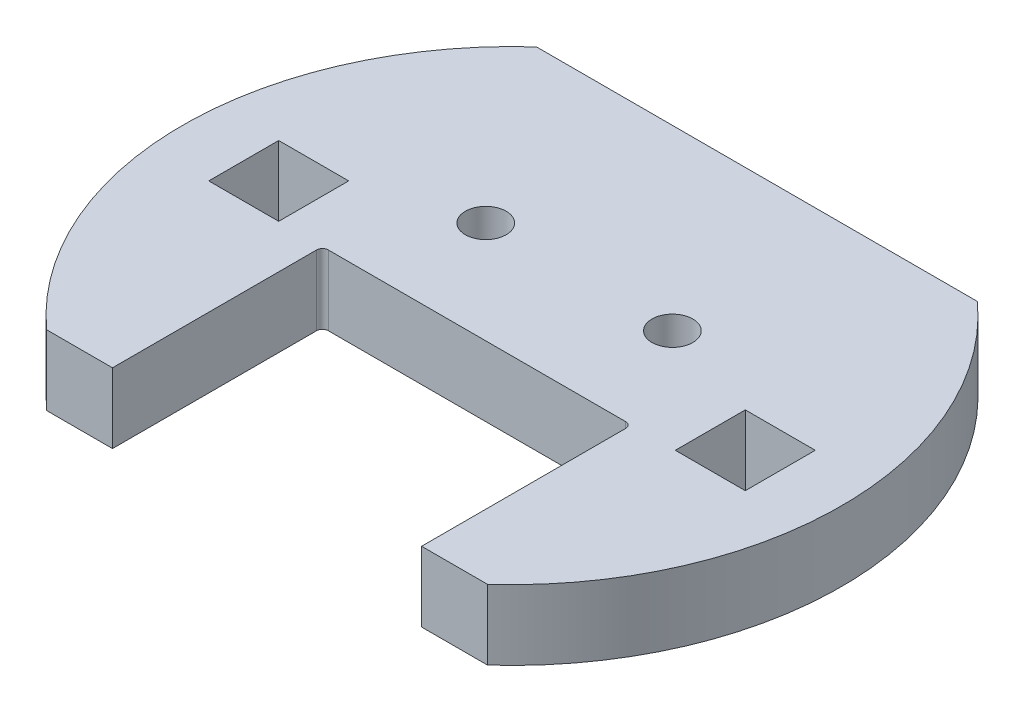
SolidWorks part; units mm, degrees
ref_plane "Alzado" through (0, 0, 0) normal (0, 0, 1) x (1, 0, 0)
ref_plane "Planta" through (0, 0, 0) normal (0, 1, 0) x (1, 0, 0)
ref_plane "Vista lateral" through (0, 0, 0) normal (1, 0, 0) x (0, 0, -1)
sketch "Croquis1" plane through (0, 0, 0) normal (0, 1, 0) x (1, 0, 0)
  line L0 (-161, 103.5) -> (-38.7919, 9.7565)
  line L1 (-40, 40) -> (40, 40) construction
  line L2 (-40, 40) -> (-40, -40) construction
  line L3 (-40, -40) -> (40, -40) construction
  line L4 (40, 40) -> (40, -40) construction
  line L5 (-40, 40) -> (40, -40) construction
  line L6 (-40, -40) -> (40, 40) construction
  line L7 (-161, 123.5) -> (161, 123.5) construction
  line L8 (-161, 123.5) -> (-161, -123.5) construction
  line L9 (-161, -123.5) -> (161, -123.5) construction
  line L10 (161, 123.5) -> (161, -123.5) construction
  line L11 (-161, 123.5) -> (161, -123.5) construction
  line L12 (-161, -123.5) -> (161, 123.5) construction
  line L13 (-161, 103.5) -> (-161, 123.5)
  line L14 (-161, 123.5) -> (-141, 123.5)
  line L15 (-141, 123.5) -> (-22.8238, 32.8493)
  line L16 (-38.7919, -9.7565) -> (-161, -103.5)
  line L17 (-161, -103.5) -> (-161, -123.5)
  line L18 (-161, -123.5) -> (-141, -123.5)
  line L19 (-141, -123.5) -> (-22.8238, -32.8493)
  line L20 (-38.7919, 9.7565) -> (-38.7919, -9.7565) construction
  line L21 (-22.8238, 32.8493) -> (-22.8238, -32.8493) construction
  line L22 (0, 40) -> (0, -40) construction
  line L23 (161, 123.5) -> (141, 123.5)
  line L24 (141, 123.5) -> (22.8238, 32.8493)
  line L25 (161, 103.5) -> (161, 123.5)
  line L26 (161, 103.5) -> (38.7919, 9.7565)
  line L27 (161, -123.5) -> (141, -123.5)
  line L28 (161, -103.5) -> (161, -123.5)
  line L29 (38.7919, -9.7565) -> (161, -103.5)
  line L30 (141, -123.5) -> (22.8238, -32.8493)
  circle A0 centre (0, 0) radius 40 construction
  arc A1 (-38.7919, 9.7565) -> (-38.7919, -9.7565) centre (0, 0) ccw
  arc A2 (-22.8238, 32.8493) -> (22.8238, 32.8493) centre (0, 0) cw
  arc A3 (22.8238, -32.8493) -> (-22.8238, -32.8493) centre (0, 0) cw
  arc A4 (38.7919, 9.7565) -> (38.7919, -9.7565) centre (0, 0) cw
  point P0 (0, 0)
  point P6 (0, 0)
  dimension "D1" = 80
  dimension "D2" = 80
  dimension "D3" = 322
  dimension "D4" = 247
  dimension "D5" = 20
extrude "Saliente-Extruir1" add sketch "Croquis1" along normal blind 6
sketch "Croquis4" plane through (0, 0, 0) normal (0, 1, 0) x (1, 0, 0)
  line L0 (-161, 103.5) -> (-161, 123.5)
  line L1 (-161, 123.5) -> (-141, 123.5)
  line L2 (-141, 123.5) -> (-141, 129.5)
  line L3 (-141, 129.5) -> (-167, 129.5)
  line L4 (-167, 129.5) -> (-167, 103.5)
  line L5 (-167, 103.5) -> (-161, 103.5)
  line L6 (-161, -103.5) -> (-161, -123.5)
  line L7 (-161, -123.5) -> (-141, -123.5)
  line L8 (-141, -123.5) -> (-141, -129.5)
  line L9 (-141, -129.5) -> (-167, -129.5)
  line L10 (-167, -129.5) -> (-167, -103.5)
  line L11 (-167, -103.5) -> (-161, -103.5)
  line L12 (0, 40) -> (0, -40) construction
  line L13 (167, -103.5) -> (161, -103.5)
  line L14 (167, -129.5) -> (167, -103.5)
  line L15 (141, -129.5) -> (167, -129.5)
  line L16 (141, -123.5) -> (141, -129.5)
  line L17 (161, -123.5) -> (141, -123.5)
  line L18 (161, -103.5) -> (161, -123.5)
  line L19 (167, 103.5) -> (161, 103.5)
  line L20 (167, 129.5) -> (167, 103.5)
  line L21 (141, 129.5) -> (167, 129.5)
  line L22 (141, 123.5) -> (141, 129.5)
  line L23 (161, 123.5) -> (141, 123.5)
  line L24 (161, 103.5) -> (161, 123.5)
  arc A0 (22.8238, 32.8493) -> (-22.8238, 32.8493) centre (0, 0) ccw construction
  arc A1 (-22.8238, -32.8493) -> (22.8238, -32.8493) centre (0, 0) ccw construction
  dimension "D1" = 6
  dimension "D2" = 6
  dimension "D3" = 6
  dimension "D4" = 6
extrude "Saliente-Extruir2" [suppressed] add sketch "Croquis4" along normal blind 12
sketch "Croquis7" plane through (0, 0, 0) normal (0, -1, 0) x (-1, 0, 0)
  circle A0 centre (0, 0) radius 40
  arc A1 (-38.7919, 9.7565) -> (-38.7919, -9.7565) centre (0, 0) ccw construction
extrude "Saliente-Extruir5" add sketch "Croquis7" along normal blind 6
sketch "Croquis5" plane through (0, -6, 0) normal (0, -1, 0) x (1, 0, 0)
  line L0 (13.25, 11) -> (-13.25, 11) construction
  line L1 (-10.25, 8) -> (10.25, 8) construction
  line L2 (-10.25, 8) -> (-10.25, -8) construction
  line L3 (-10.25, -8) -> (10.25, -8) construction
  line L4 (10.25, 8) -> (10.25, -8) construction
  line L5 (-10.25, 8) -> (10.25, -8) construction
  line L6 (-10.25, -8) -> (10.25, 8) construction
  line L7 (-13.25, 11) -> (-13.25, -11) construction
  line L8 (-13.25, -11) -> (13.25, -11) construction
  line L9 (13.25, -11) -> (13.25, -21) construction
  line L10 (13.25, -21) -> (-28.25, -21) construction
  line L11 (-28.25, -21) -> (-28.25, 21) construction
  line L12 (-28.25, 21) -> (13.25, 21) construction
  line L13 (13.25, 21) -> (13.25, 11) construction
  line L14 (0, 11) -> (0, 0) construction
  line L15 (0, 0) -> (0, -11) construction
  line L16 (13.25, 11) -> (28.25, 11) construction
  line L17 (-28.25, 21) -> (28.25, 21) construction
  line L18 (-28.25, 21) -> (-28.25, -21) construction
  line L19 (-28.25, -21) -> (28.25, -21) construction
  line L20 (28.25, 21) -> (28.25, -21) construction
  line L21 (-28.25, 21) -> (28.25, -21) construction
  line L22 (-28.25, -21) -> (28.25, 21) construction
  line L23 (28.25, 11) -> (28.25, 21) construction
  line L24 (28.25, 21) -> (13.25, 21) construction
  line L25 (13.25, -21) -> (28.25, -21) construction
  line L26 (28.25, -21) -> (28.25, -11) construction
  line L27 (28.25, -11) -> (13.25, -11) construction
  line L28 (-9, 7) -> (9, 7) construction
  line L29 (0, 7) -> (0, 0) construction
  line L30 (-9, 7) -> (9, 7) construction
  line L31 (-9, 7.5) -> (9, 7.5) construction
  line L32 (-9, 6.5) -> (9, 6.5) construction
  line L33 (-18.8961, 21) -> (18.8961, 21) construction
  line L34 (18.8961, -21) -> (-18.8961, -21)
  line L35 (-18.8961, 21) -> (-13.25, 21)
  line L36 (-13.25, 21) -> (-13.25, -11)
  line L37 (-13.25, -11) -> (13.25, -11)
  line L38 (13.25, -11) -> (13.25, 21)
  line L39 (13.25, 21) -> (18.8961, 21)
  line L40 (-8, -5.75) -> (8, -5.75) construction
  arc A0 (-9, 7.5) -> (-9, 6.5) centre (-9, 7) ccw construction
  arc A1 (9, 6.5) -> (9, 7.5) centre (9, 7) ccw construction
  arc A2 (-18.8961, 21) -> (-18.8961, -21) centre (0, 0) ccw
  arc A3 (18.8961, 21) -> (18.8961, -21) centre (0, 0) cw
  circle A4 centre (-8, -5.75) radius 1.75 construction
  circle A5 centre (8, -5.75) radius 1.75 construction
  point P0 (0, 0)
  point P26 (0, 7)
  dimension "D11" = 0.5
  dimension "D12" = 3.5
  dimension "D14" = 2.25
  dimension "D1" = 16
  dimension "D2" = 20.5
  dimension "D3" = 3
  dimension "D4" = 3
  dimension "D5" = 10
  dimension "D6" = 10
  dimension "D7" = 15
  dimension "D8" = 3
  dimension "D9" = 18
  dimension "D10" = 1
  dimension "D13" = 2.25
  dimension "D15" = 2.25
extrude "Saliente-Extruir3" add sketch "Croquis5" along normal blind 6
sketch "Croquis6" plane through (0, -12, 0) normal (0, -1, 0) x (1, 0, 0)
  line L0 (18.8961, 21) -> (13.25, 21) construction
  line L1 (-28.25, 21) -> (28.25, 21) construction
  line L2 (-28.25, 21) -> (-28.25, -21) construction
  line L3 (-28.25, -21) -> (28.25, -21) construction
  line L4 (28.25, 21) -> (28.25, -21) construction
  line L5 (-28.25, 21) -> (28.25, -21) construction
  line L6 (-28.25, -21) -> (28.25, 21) construction
  line L7 (-18.8961, 21) -> (-13.25, 21)
  line L8 (-9, 7) -> (9, 7) construction
  line L9 (-9, 7.5) -> (9, 7.5) construction
  line L10 (-9, 6.5) -> (9, 6.5) construction
  line L11 (-18.8961, 21) -> (18.8961, 21) construction
  line L12 (18.8961, -21) -> (-18.8961, -21) construction
  line L18 (13.25, 21) -> (18.8961, 21)
  line L19 (18.8961, -21) -> (-18.8961, -21)
  line L20 (-13.25, 21) -> (-13.25, 3.5)
  line L21 (-13.25, 21) -> (-13.25, -11) construction
  line L22 (-12.75, 3) -> (12.75, 3)
  line L23 (13.25, -11) -> (13.25, 21) construction
  line L24 (13.25, 3.5) -> (13.25, 21)
  line L25 (-13.25, 3.5) -> (13.25, 3.5) construction
  arc A0 (-9, 7.5) -> (-9, 6.5) centre (-9, 7) ccw construction
  arc A1 (9, 6.5) -> (9, 7.5) centre (9, 7) ccw construction
  arc A2 (9, 6.5) -> (9, 7.5) centre (9, 7) ccw construction
  circle A3 centre (0, 0) radius 28.25 construction
  arc A4 (18.8961, 21) -> (18.8961, -21) centre (0, 0) cw construction
  arc A5 (-18.8961, -21) -> (-18.8961, 21) centre (0, 0) cw construction
  arc A6 (-18.8961, 21) -> (-18.8961, -21) centre (0, 0) ccw construction
  arc A7 (-18.8961, -21) -> (-18.8961, 21) centre (0, 0) cw
  arc A8 (18.8961, -21) -> (18.8961, 21) centre (0, 0) ccw
  circle A9 centre (-8, -5.75) radius 1.75
  circle A10 centre (8, -5.75) radius 1.75
  circle A11 centre (-8, -5.75) radius 1.75 construction
  circle A12 centre (8, -5.75) radius 1.75 construction
  arc A13 (-13.25, 3.5) -> (-12.75, 3) centre (-12.75, 3.5) ccw
  arc A14 (12.75, 3) -> (13.25, 3.5) centre (12.75, 3.5) ccw
  point P0 (0, 0)
  point P14 (0, 7)
  dimension "D2" = 0.5
  dimension "D1" = 18
extrude "Saliente-Extruir4" add sketch "Croquis6" along normal blind 6
sketch "Croquis8" plane through (0, -18, 0) normal (0, -1, 0) x (1, 0, 0)
  line L0 (-20, 0) -> (0, 0) construction
  line L1 (-23, 3) -> (-17, 3)
  line L2 (-23, 3) -> (-23, -3)
  line L3 (-23, -3) -> (-17, -3)
  line L4 (-17, 3) -> (-17, -3)
  line L5 (-23, 3) -> (-17, -3) construction
  line L6 (-23, -3) -> (-17, 3) construction
  line L7 (0, 0) -> (0, -21) construction
  line L8 (-18.8961, -21) -> (18.8961, -21) construction
  line L9 (23, -3) -> (17, -3)
  line L10 (23, 3) -> (23, -3)
  line L11 (23, 3) -> (17, 3)
  line L12 (17, 3) -> (17, -3)
  point P0 (-20, 0)
  dimension "D1" = 6
  dimension "D2" = 6
  dimension "D3" = 20
extrude "Cortar-Extruir1" cut sketch "Croquis8" against normal through all
sketch "Croquis9" plane through (0, 6, 0) normal (0, 1, 0) x (1, 0, 0)
  line L1 (-161, 123.5) -> (161, 123.5)
  line L2 (-161, 123.5) -> (-161, -123.5)
  line L3 (-161, -123.5) -> (161, -123.5)
  line L4 (161, 123.5) -> (161, -123.5)
  line L5 (-161, 123.5) -> (161, -123.5) construction
  line L6 (-161, -123.5) -> (161, 123.5) construction
  point P0 (0, 0)
extrude "Cortar-Extruir2" cut sketch "Croquis9" against normal blind 12
sketch "Croquis10" plane through (0, -6, 0) normal (0, 1, 0) x (1, 0, 0)
  circle A0 centre (0, 0) radius 28.25
  arc A1 (18.8961, -21) -> (18.8961, 21) centre (0, 0) ccw construction
extrude "Cortar-Extruir3" cut sketch "Croquis10" against normal blind 6
